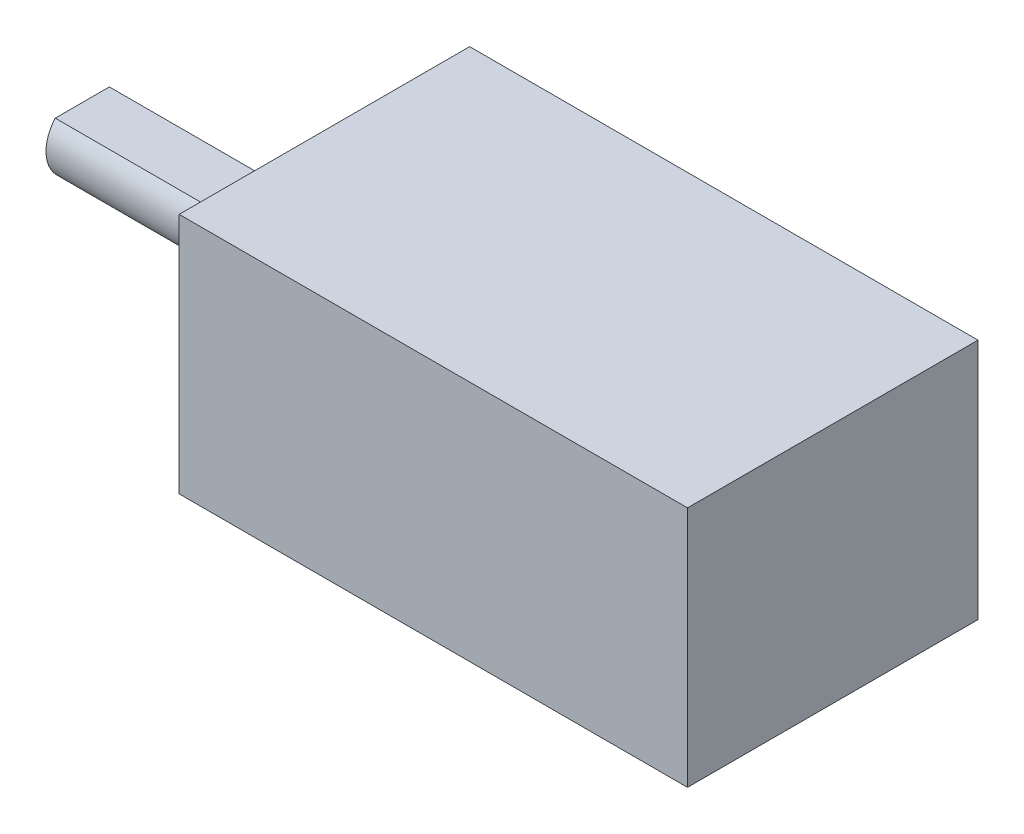
SolidWorks part; units mm, degrees
ref_plane "Front Plane" through (0, 0, 0) normal (0, 0, 1) x (1, 0, 0)
ref_plane "Top Plane" through (0, 0, 0) normal (0, 1, 0) x (1, 0, 0)
ref_plane "Right Plane" through (0, 0, 0) normal (1, 0, 0) x (0, 0, -1)
sketch "Sketch1" plane through (0, 0, 0) normal (0, 1, 0) x (1, 0, 0)
  line L1 (0, 0) -> (21, 0)
  line L2 (0, 0) -> (0, 12)
  line L3 (0, 12) -> (21, 12)
  line L4 (21, 0) -> (21, 12)
  line L5 (0, 0) -> (21, 12) construction
  line L6 (0, 12) -> (21, 0) construction
  point P4 (10.5, 6)
  dimension "D1" = 12
  dimension "D2" = 21
extrude "Boss-Extrude1" add sketch "Sketch1" along normal blind 10
sketch "Sketch2" plane through (0, 0, 0) normal (-1, 0, 0) x (0, 0, 1)
  line L0 (-12, 10) -> (0, 0) construction
  line L1 (-7.118, 6) -> (-4.882, 6)
  line L2 (-6, 6) -> (-6, 3.5) construction
  circle A0 centre (-6, 5) radius 1.5 construction
  arc A1 (-7.118, 6) -> (-4.882, 6) centre (-6, 5) ccw
  dimension "D1" = 3
  dimension "D2" = 2.5
extrude "Boss-Extrude2" add sketch "Sketch2" along normal blind 10
